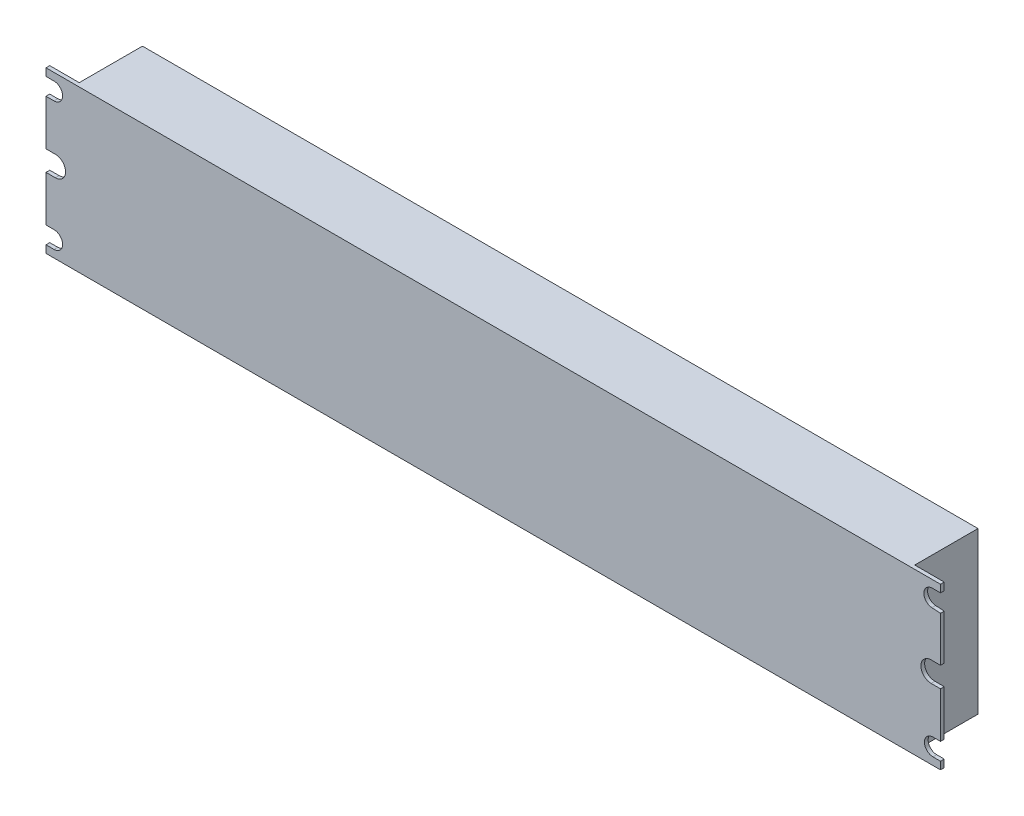
SolidWorks part; units mm, degrees
ref_plane "Front Plane" through (0, 0, 0) normal (0, 0, 1) x (1, 0, 0)
ref_plane "Top Plane" through (0, 0, 0) normal (0, 1, 0) x (1, 0, 0)
ref_plane "Right Plane" through (0, 0, 0) normal (1, 0, 0) x (0, 0, -1)
sketch "Sketch1" plane through (0, 0, 0) normal (0, 1, 0) x (1, 0, 0)
  line L1 (0, 0) -> (423.926, 0)
  line L2 (0, 0) -> (0, 31.75)
  line L3 (0, 31.75) -> (423.926, 31.75)
  line L4 (423.926, 0) -> (423.926, 31.75)
  dimension "D1" = 423.926
  dimension "1.25" = 31.75
extrude "Boss-Extrude1" add sketch "Sketch1" along normal blind 76.2
sketch "Sketch5" plane through (0, 0, -31.75) normal (0, 0, -1) x (-1, 0, 0)
  line L0 (-423.926, 0) -> (0, 0) construction
  line L1 (-423.926, 76.2) -> (-409.956, 76.2)
  line L2 (-423.926, 76.2) -> (-423.926, 0)
  line L3 (-423.926, 0) -> (-409.956, 0)
  line L4 (-409.956, 76.2) -> (-409.956, 0)
  line L5 (-423.926, 76.2) -> (0, 76.2) construction
  line L6 (0, 0) -> (-13.97, 0)
  line L7 (0, 0) -> (0, 76.2)
  line L8 (0, 76.2) -> (-13.97, 76.2)
  line L9 (-13.97, 0) -> (-13.97, 76.2)
  dimension "D1" = 395.986
extrude "Cut-Extrude5" cut sketch "Sketch5" against normal blind 29.972
sketch "Sketch6" plane through (0, 0, -1.778) normal (0, 0, -1) x (-1, 0, 0)
  line L0 (-13.97, 0) -> (0, 0) construction
  line L2 (-409.956, 76.2) -> (-423.926, 76.2) construction
  line L3 (0, 76.2) -> (-13.97, 76.2) construction
  line L4 (-423.926, 0) -> (-409.956, 0) construction
  line L6 (0, 0) -> (0, 76.2) construction
  line L7 (-423.926, 76.2) -> (-423.926, 0) construction
  circle A0 centre (-3.81, 7.62) radius 4.064
  circle A1 centre (-3.81, 68.58) radius 4.064
  circle A2 centre (-4.445, 38.1) radius 4.826
  circle A3 centre (-420.37, 7.62) radius 4.064
  circle A4 centre (-420.116, 68.58) radius 4.064
  circle A5 centre (-419.481, 38.1) radius 4.826
  dimension "D1" = 7.62
  dimension "D2" = 3.81
  dimension "D5" = 7.62
  dimension "D6" = 7.62
  dimension "D7" = 38.1
  dimension "D8" = 38.1
  dimension "D3" = 416.56
  dimension "D12" = 3.81
  dimension "D13" = 4.445
  dimension "D4" = 7.62
  dimension "D10" = 3.81
  dimension "D14" = 4.445
extrude "Cut-Extrude6" cut sketch "Sketch6" against normal blind 416.56
sketch "Sketch8" plane through (0, 0, -1.778) normal (0, 0, -1) x (-1, 0, 0)
  line L0 (-419.862, 72.6361) -> (-423.926, 72.6361)
  line L1 (-423.926, 76.2) -> (-423.926, 69.9942) construction
  line L2 (0, 76.2) -> (-423.926, 76.2) construction
  line L3 (-423.926, 72.6361) -> (-423.926, 69.9942)
  line L4 (-423.926, 69.9942) -> (-419.862, 72.6361)
  line L5 (-419.862, 64.5239) -> (-423.926, 64.2694)
  line L6 (-423.926, 67.1658) -> (-423.926, 39.9794) construction
  line L7 (-423.926, 64.2694) -> (-423.926, 67.1658)
  line L8 (-423.926, 67.1658) -> (-419.862, 64.5239)
  line L9 (-419.481, 42.926) -> (-423.926, 42.926)
  line L10 (-423.926, 42.926) -> (-423.926, 39.9794)
  line L11 (-423.926, 39.9794) -> (-419.481, 42.926)
  line L12 (-419.481, 33.274) -> (-423.926, 33.274)
  line L13 (-423.926, 36.2206) -> (-423.926, 9.5875) construction
  line L14 (-423.926, 33.274) -> (-423.926, 36.2206)
  line L15 (-423.926, 36.2206) -> (-419.481, 33.274)
  line L16 (-420.37, 11.684) -> (-423.926, 11.684)
  line L17 (-423.926, 11.684) -> (-423.926, 9.5875)
  line L18 (-423.926, 9.5875) -> (-420.37, 11.684)
  line L19 (-420.37, 3.556) -> (-423.926, 3.556)
  line L20 (-423.926, 5.6525) -> (-423.926, 0) construction
  line L21 (-423.926, 3.556) -> (-423.926, 5.6525)
  line L22 (-423.926, 5.6525) -> (-420.37, 3.556)
  line L23 (-3.81, 72.644) -> (0, 72.644)
  line L24 (0, 69.9942) -> (0, 76.2) construction
  line L25 (0, 72.644) -> (0, 69.9942)
  line L26 (0, 69.9942) -> (-3.81, 72.644)
  line L27 (-3.81, 64.516) -> (0, 64.516)
  line L28 (0, 39.9794) -> (0, 67.1658) construction
  line L29 (0, 64.516) -> (0, 67.1658)
  line L30 (0, 67.1658) -> (-3.81, 64.516)
  line L31 (-4.445, 42.926) -> (0, 42.926)
  line L32 (0, 42.926) -> (0, 39.9794)
  line L33 (0, 39.9794) -> (-4.445, 42.926)
  line L34 (-4.445, 33.274) -> (0, 33.274)
  line L35 (0, 9.0342) -> (0, 36.2206) construction
  line L36 (0, 33.274) -> (0, 36.2206)
  line L37 (0, 36.2206) -> (-4.445, 33.274)
  line L38 (-3.81, 11.684) -> (0, 11.684)
  line L39 (0, 11.684) -> (0, 9.0342)
  line L40 (0, 9.0342) -> (-3.81, 11.684)
  line L41 (-3.81, 3.556) -> (0, 3.556)
  line L42 (0, 0) -> (0, 6.2058) construction
  line L43 (0, 3.556) -> (0, 6.2058)
  line L44 (0, 6.2058) -> (-3.81, 3.556)
  arc A0 (-423.926, 67.1658) -> (-423.926, 69.9942) centre (-420.116, 68.58) ccw construction
  arc A1 (-423.926, 36.2206) -> (-423.926, 39.9794) centre (-419.481, 38.1) ccw construction
  arc A2 (-423.926, 5.6525) -> (-423.926, 9.5875) centre (-420.37, 7.62) ccw construction
  arc A3 (0, 69.9942) -> (0, 67.1658) centre (-3.81, 68.58) ccw construction
  arc A4 (0, 39.9794) -> (0, 36.2206) centre (-4.445, 38.1) ccw construction
  arc A5 (0, 9.0342) -> (0, 6.2058) centre (-3.81, 7.62) ccw construction
  dimension "D1" = 4.064
  dimension "D2" = 0
extrude "Cut-Extrude7" cut sketch "Sketch8" against normal through all
